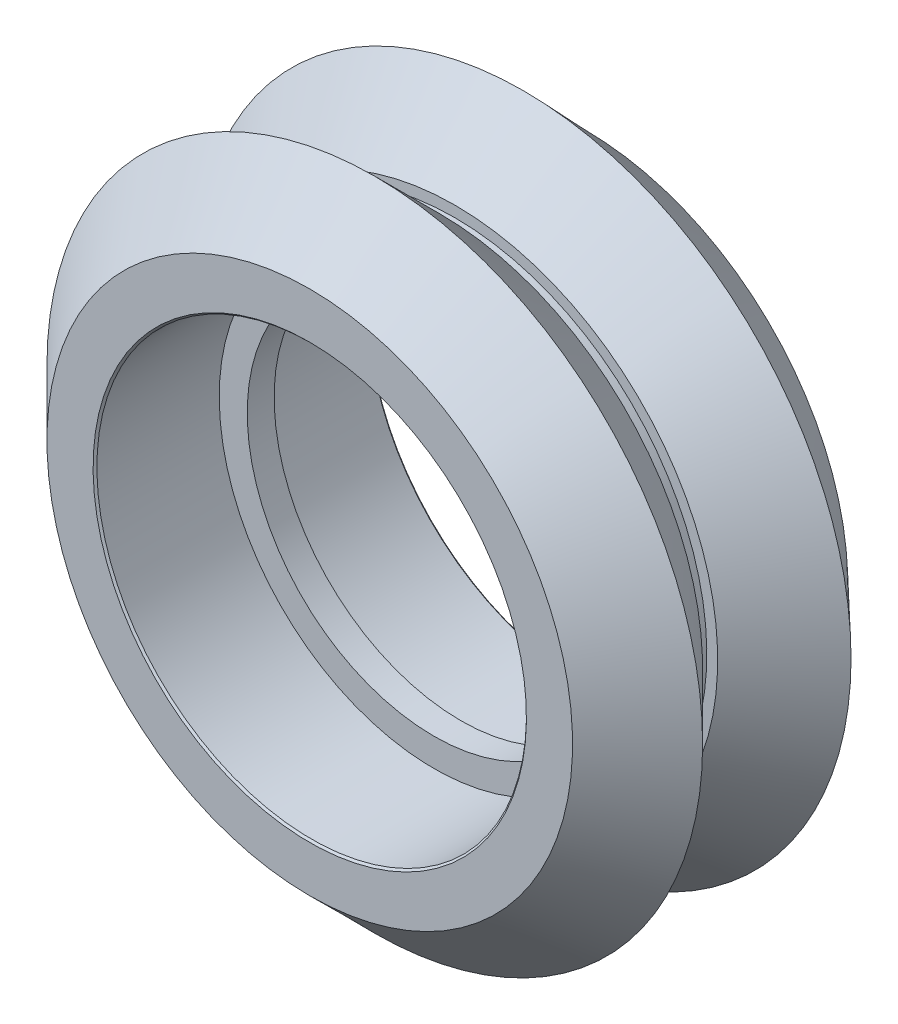
SolidWorks part; units mm, degrees
ref_plane "Front Plane" through (0, 0, 0) normal (0, 0, 1) x (1, 0, 0)
ref_plane "Top Plane" through (0, 0, 0) normal (0, 1, 0) x (1, 0, 0)
ref_plane "Right Plane" through (0, 0, 0) normal (1, 0, 0) x (0, 0, -1)
sketch "Sketch2" plane through (0, 0, 0) normal (1, 0, 0) x (0, 0, -1)
  line L0 (2.6363, 12.3213) -> (2.6363, -11.9787) construction
  dimension "D1" = 24.3
sketch "Sketch3" plane through (0, 0, 0) normal (1, 0, 0) x (0, 0, -1)
  line L0 (-0.505, 6.945) -> (0.495, 6.945)
  line L1 (0.495, 6.945) -> (0.495, 7.987)
  line L2 (0.495, 7.987) -> (5.0443, 7.987)
  line L3 (5.0443, 7.987) -> (5.115, 8.0577)
  line L4 (5.115, 8.0577) -> (5.115, 9.77)
  line L5 (5.115, 9.77) -> (2.8175, 12.1869)
  line L6 (2.8175, 12.1869) -> (0.275, 9.77)
  line L7 (0.275, 9.77) -> (0.265, 9.375)
  line L8 (0.265, 9.375) -> (-0.285, 9.375)
  line L9 (-0.285, 9.375) -> (-0.285, 9.77)
  line L10 (-0.285, 9.77) -> (-2.7067, 12.1917)
  line L11 (-2.7067, 12.1917) -> (-5.125, 9.7734)
  line L12 (-5.125, 9.7734) -> (-5.125, 8.0577)
  line L13 (-5.125, 8.0577) -> (-5.0543, 7.987)
  line L15 (-5.0543, 7.987) -> (-0.505, 7.987)
  line L16 (-0.505, 7.987) -> (-0.505, 6.945)
  dimension "D1" = 45
  dimension "D2" = 0.1
  dimension "D3" = 4.62
  dimension "D4" = 45
  dimension "D5" = 4.62
  dimension "D6" = 1
  dimension "D7" = 4.84
  dimension "D8" = 4.84
  dimension "D9" = 45
  dimension "D10" = 0.55
  dimension "D11" = 9.77
  dimension "D12" = 45
  dimension "D13" = 5.115
  dimension "D14" = 9.77
  dimension "D15" = 9.375
  dimension "D16" = 3.42
  dimension "D17" = 6.945
  dimension "D18" = 7.987
  dimension "D19" = 0.1
  dimension "D20" = 12.1869
sketch "Sketch4" plane through (0, 0, 0) normal (0, 0, 1) x (1, 0, 0)
  circle A0 centre (0, 0) radius 2.5
  dimension "D1" = 5
sweep "Sweep1" add profiles "Sketch3" path "Sketch4"
